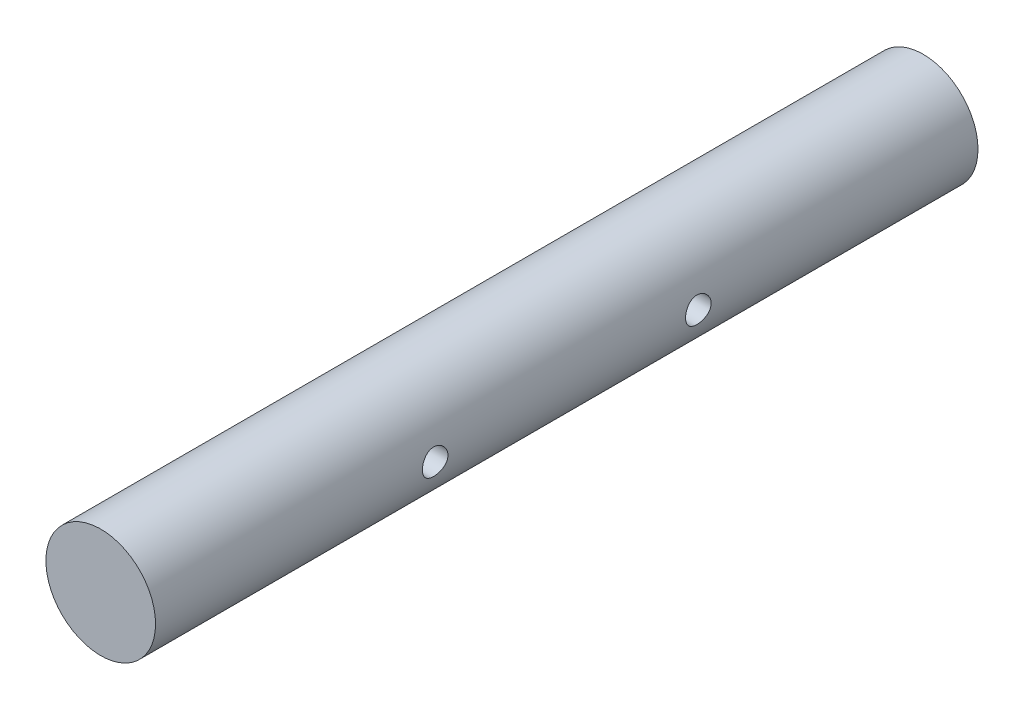
SolidWorks part; units mm, degrees
material "Plain Carbon Steel"
ref_plane "Front Plane" through (0, 0, 0) normal (0, 0, 1) x (1, 0, 0)
ref_plane "Top Plane" through (0, 0, 0) normal (0, 1, 0) x (1, 0, 0)
ref_plane "Right Plane" through (0, 0, 0) normal (1, 0, 0) x (0, 0, -1)
sketch "Sketch1" plane through (0, 0, 0) normal (0, 0, 1) x (1, 0, 0)
  circle A0 centre (0, 0) radius 30
  dimension "D1" = 60
extrude "Boss-Extrude1" add sketch "Sketch1" along normal mid plane 450
sketch "Sketch2" plane through (0, 0, 0) normal (1, 0, 0) x (0, 0, -1)
  line L0 (-225, 0) -> (225, 0) construction
  line L1 (-225, 30) -> (-225, -30) construction
  line L2 (225, -30) -> (225, 30) construction
  line L3 (0, 0) -> (0, 30) construction
  line L4 (225, 30) -> (-225, 30) construction
  circle A0 centre (72, 0) radius 7
  circle A1 centre (-72, 0) radius 7
  dimension "D1" = 14
  dimension "D2" = 72
extrude "Cut-Extrude1" cut sketch "Sketch2" against normal through all and the other way through all
